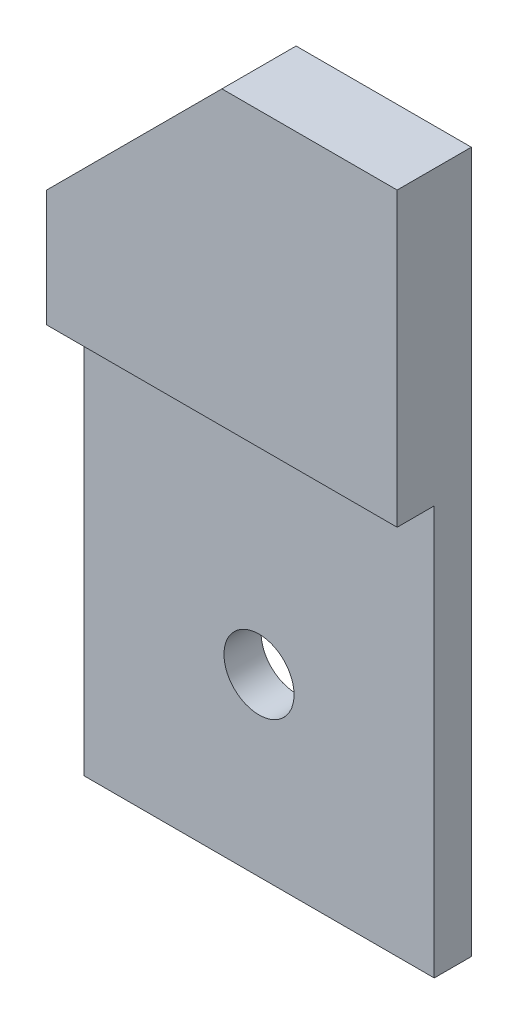
SolidWorks part; units mm, degrees
ref_plane "Front Plane" through (0, 0, 0) normal (0, 0, 1) x (1, 0, 0)
ref_plane "Top Plane" through (0, 0, 0) normal (0, 1, 0) x (1, 0, 0)
ref_plane "Right Plane" through (0, 0, 0) normal (1, 0, 0) x (0, 0, -1)
sketch "Sketch1" plane through (0, 0, 0) normal (0, 0, 1) x (1, 0, 0)
  line L0 (15, 60) -> (0, 45)
  line L1 (0, 0) -> (30, 0)
  line L2 (0, 0) -> (0, 45)
  line L3 (15, 60) -> (30, 60)
  line L4 (30, 0) -> (30, 60)
  circle A0 centre (15, 15) radius 3
  dimension "D3" = 6
  dimension "D2" = 30
  dimension "D4" = 15
extrude "Boss-Extrude1" add sketch "Sketch1" along normal blind 3.175
sketch "Sketch2" plane through (0, 0, 3.175) normal (0, 0, 1) x (1, 0, 0)
  line L7 (0, 45) -> (0, 35)
  line L8 (0, 35) -> (30, 35)
  line L9 (30, 45) -> (30, 35)
  line L10 (0, 45) -> (0, 0)
  line L11 (0, 0) -> (30, 0)
  line L12 (30, 0) -> (30, 60)
  line L13 (30, 60) -> (15, 60)
  line L14 (15, 60) -> (0, 45)
  line L15 (0, 45) -> (0, 0)
  line L16 (0, 0) -> (30, 0)
  line L17 (30, 0) -> (30, 60)
  line L18 (30, 60) -> (15, 60)
  line L19 (15, 60) -> (0, 45)
  line M6 (0, 45) -> (0, 0)
  line M8 (30, 0) -> (30, 60)
  line M9 (30, 60) -> (15, 60)
  line M10 (15, 60) -> (0, 45)
  dimension "D2" = 10
  dimension "D1" = 0
extrude "Boss-Extrude2" add sketch "Sketch2" along normal blind 3.175 contours L8 M6 M8 M9 M10
